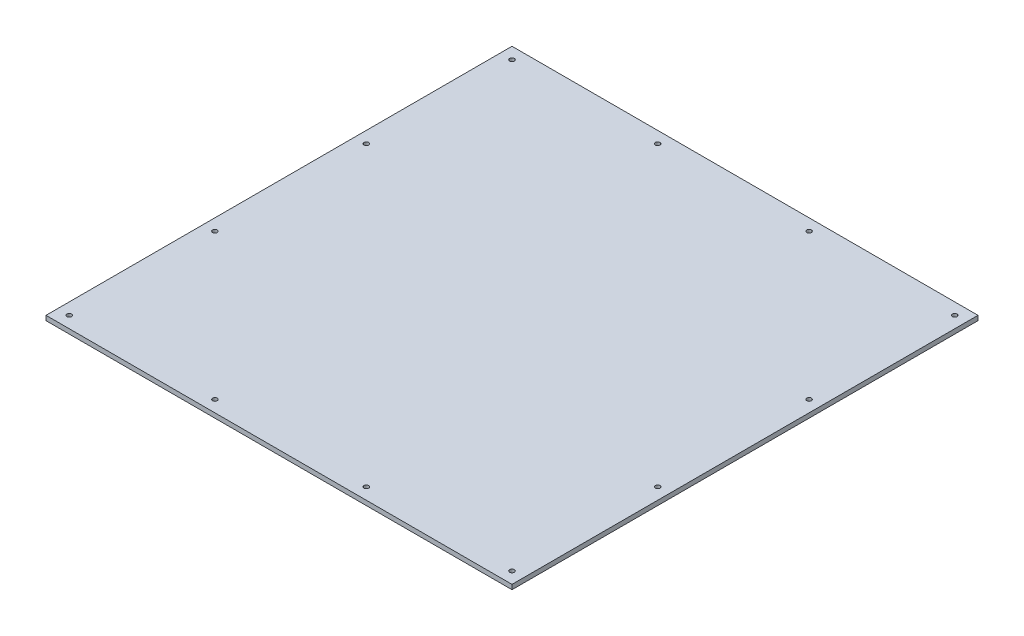
SolidWorks part; units mm, degrees
ref_plane "Front Plane" through (0, 0, 0) normal (0, 0, 1) x (1, 0, 0)
ref_plane "Top Plane" through (0, 0, 0) normal (0, 1, 0) x (1, 0, 0)
ref_plane "Right Plane" through (0, 0, 0) normal (1, 0, 0) x (0, 0, -1)
sketch "Sketch1" plane through (0, 0, 0) normal (0, 1, 0) x (1, 0, 0)
  line L1 (-200, -200) -> (200, -200)
  line L2 (-200, -200) -> (-200, 200)
  line L3 (-200, 200) -> (200, 200)
  line L4 (200, -200) -> (200, 200)
  line L5 (-200, -200) -> (200, 200) construction
  line L6 (-200, 200) -> (200, -200) construction
  circle A0 centre (-190, -190) radius 2
  circle A1 centre (-65, -190) radius 2
  circle A2 centre (65, -190) radius 2
  circle A3 centre (190, -190) radius 2
  circle A4 centre (-190, 190) radius 2
  circle A5 centre (-190, 65) radius 2
  circle A6 centre (-190, -65) radius 2
  circle A7 centre (190, 190) radius 2
  circle A8 centre (65, 190) radius 2
  circle A9 centre (-65, 190) radius 2
  circle A10 centre (190, 65) radius 2
  circle A11 centre (190, -65) radius 2
  point P0 (0, 0)
  dimension "D3" = 10
  dimension "D4" = 10
  dimension "D5" = 4
  dimension "D6" = 125
  dimension "D7" = 130
  dimension "D8" = 125
  dimension "D9" = 10
  dimension "D10" = 10
  dimension "D11" = 10
  dimension "D12" = 10
  dimension "D13" = 4
  dimension "D14" = 4
  dimension "D15" = 4
  dimension "D1" = 400
  dimension "D2" = 400
extrude "Boss-Extrude1" add sketch "Sketch1" along normal blind 4
